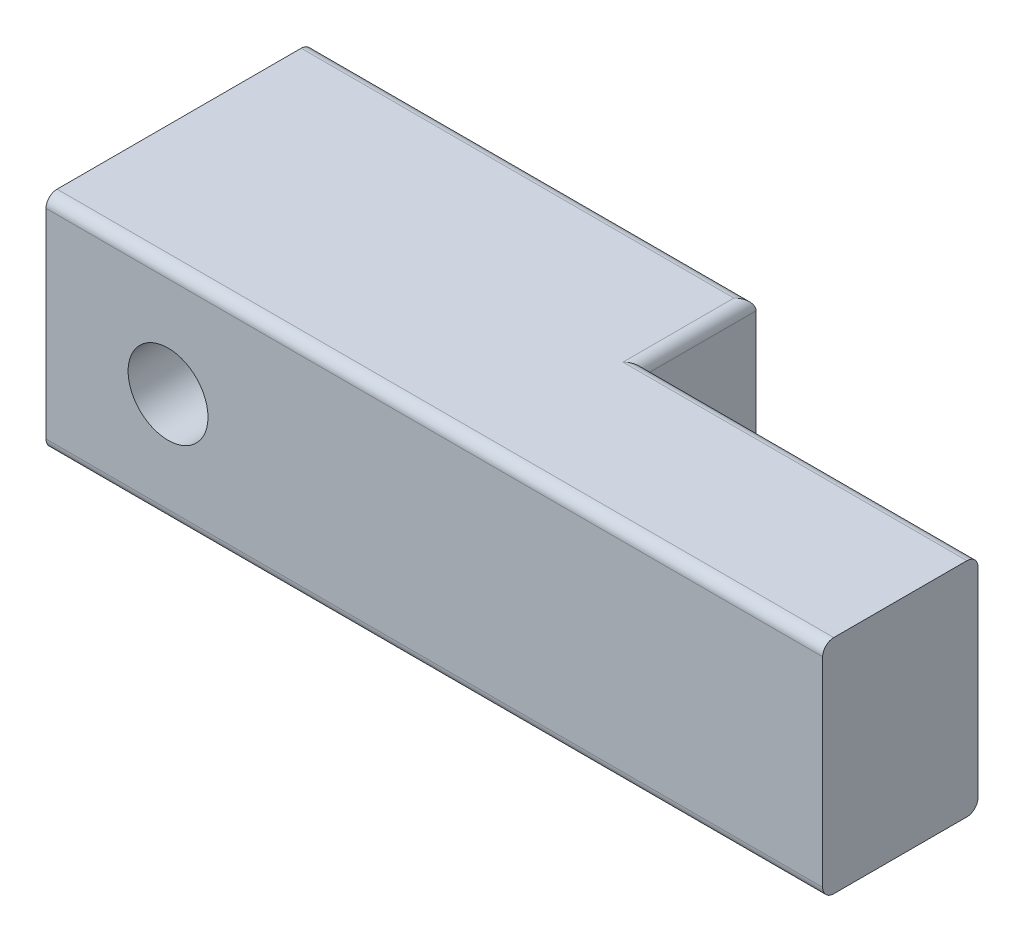
SolidWorks part; units mm, degrees
material "PLA"
ref_plane "Front Plane" through (0, 0, 0) normal (0, 0, 1) x (1, 0, 0)
ref_plane "Top Plane" through (0, 0, 0) normal (0, 1, 0) x (1, 0, 0)
ref_plane "Right Plane" through (0, 0, 0) normal (1, 0, 0) x (0, 0, -1)
sketch "Sketch1" plane through (0, 0, 0) normal (0, 0, 1) x (1, 0, 0)
  line L1 (-17.5, -5) -> (17.5, -5)
  line L2 (-17.5, -5) -> (-17.5, 5)
  line L3 (-17.5, 5) -> (17.5, 5)
  line L4 (17.5, -5) -> (17.5, 5)
  line L5 (-17.5, -5) -> (17.5, 5) construction
  line L6 (-17.5, 5) -> (17.5, -5) construction
  point P0 (0, 0)
  dimension "D1" = 35
  dimension "D2" = 10
extrude "Boss-Extrude1" add sketch "Sketch1" along normal blind 7
sketch "Sketch2" plane through (0, 0, 0) normal (0, 0, -1) x (-1, 0, 0)
  line L0 (17.5, -5) -> (-17.5, -5) construction
  line L1 (17.5, 5) -> (-2.5, 5)
  line L2 (17.5, 5) -> (17.5, -5)
  line L3 (17.5, -5) -> (-2.5, -5)
  line L4 (-2.5, 5) -> (-2.5, -5)
  dimension "D1" = 20
extrude "Boss-Extrude2" add sketch "Sketch2" along normal blind 5
sketch "Sketch5" plane through (0, 0, 7) normal (0, 0, 1) x (1, 0, 0)
  line L0 (-17.5, 5) -> (-17.5, -5) construction
  circle A0 centre (-12, 0) radius 1.5
  dimension "D1" = 3
  dimension "D2" = 5.5
fillet "Fillet1" radius 0.5 8 edges at (2.5, -5, -2.5) (2.5, 5, -2.5) (10, 5, 0) (10, -5, 0) (-7.5, -5, -5) (-7.5, 5, -5) (0, -5, 7) (0, 5, 7)
hole_wizard "Ø3.6 (3.6) Diameter Hole1" positions "3DSketch1" profile "Sketch16" hole size "Ø3.6" standard "ANSI Metric" end condition through all
sketch3d "3DSketch1"
  point P0 (-12, 0, 7)
sketch "Sketch16" plane through (-12, 0, 7) normal (1, 0, 0) x (0, -1, 0)
  line L0 (0, 0) -> (0, 12)
  line L1 (0, 12) -> (1.8, 12)
  line L2 (1.8, 12) -> (1.8, 0)
  line L5 (1.8, 0) -> (0, 0)
  line L11 (0, -6.35) -> (0, 107.95) construction
  dimension "Thru Hole Dia." = 3.6
  dimension "Thru Hole Depth" = 12
